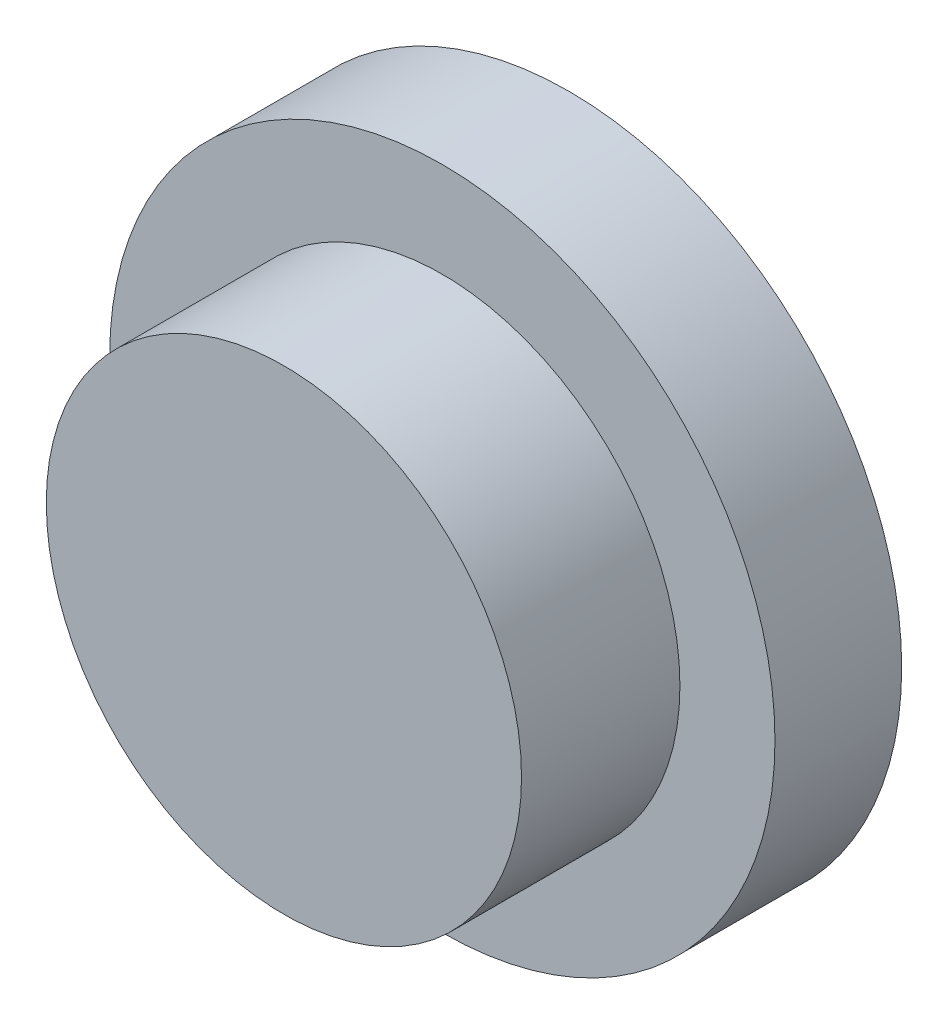
SolidWorks part; units mm, degrees
ref_plane "Front Plane" through (0, 0, 0) normal (0, 0, 1) x (1, 0, 0)
ref_plane "Top Plane" through (0, 0, 0) normal (0, 1, 0) x (1, 0, 0)
ref_plane "Right Plane" through (0, 0, 0) normal (1, 0, 0) x (0, 0, -1)
sketch "Sketch1" plane through (0, 0, 0) normal (0, 0, 1) x (1, 0, 0)
  circle A0 centre (0, 0) radius 7.5
  dimension "D1" = 15
extrude "Boss-Extrude1" add sketch "Sketch1" along normal blind 5
sketch "Sketch2" plane through (0, 0, 5) normal (0, 0, 1) x (1, 0, 0)
  circle A0 centre (0, 0) radius 7.5
  dimension "D1" = 15
sketch "Sketch3" plane through (0, 0, 0) normal (0, 0, -1) x (-1, 0, 0)
  circle A0 centre (0, 0) radius 10.5
  dimension "D1" = 21
extrude "Boss-Extrude2" add sketch "Sketch3" along normal blind 4
sketch "Sketch4" plane through (0, 0, -4) normal (0, 0, -1) x (-1, 0, 0)
  circle A0 centre (0, 0) radius 8.25
  dimension "D1" = 16.5
extrude "Cut-Extrude1" cut sketch "Sketch4" against normal blind 3
chamfer "Chamfer1" distance 0.5 angle 45 1 edges at (-8.25, 0, -4)
